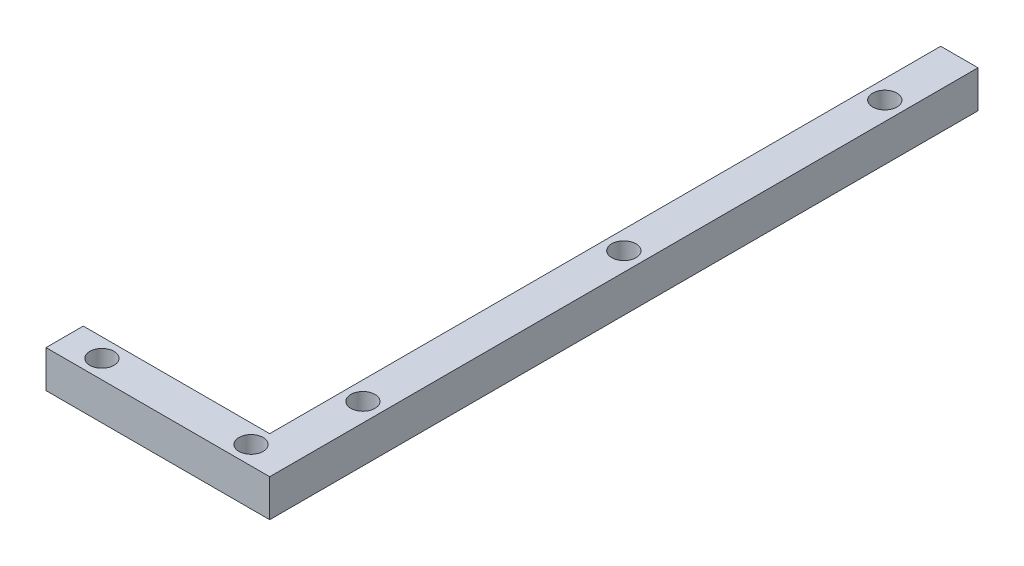
SolidWorks part; units mm, degrees
ref_plane "Front Plane" through (0, 0, 0) normal (0, 0, 1) x (1, 0, 0)
ref_plane "Top Plane" through (0, 0, 0) normal (0, 1, 0) x (1, 0, 0)
ref_plane "Right Plane" through (0, 0, 0) normal (1, 0, 0) x (0, 0, -1)
sketch "Sketch1" plane through (0, 0, 0) normal (0, 1, 0) x (1, 0, 0)
  line L0 (0, 0) -> (0, 180)
  line L1 (0, 180) -> (10, 180)
  line L2 (10, 180) -> (10, -10)
  line L3 (10, -10) -> (-50, -10)
  line L4 (-50, -10) -> (-50, 0)
  line L5 (-50, 0) -> (0, 0)
  dimension "D1" = 10
  dimension "D2" = 10
  dimension "D3" = 180
  dimension "D4" = 60
extrude "Boss-Extrude1" add sketch "Sketch1" along normal blind 10 contours L2 L3 L4 L5 L0 L1
sketch "Sketch2" plane through (0, 10, 0) normal (0, 1, 0) x (1, 0, 0)
  line L0 (0, 180) -> (10, 180) construction
  line L1 (-50, 0) -> (0, 0) construction
  line L2 (10, 180) -> (10, -10) construction
  line L3 (-50, -10) -> (-50, 0) construction
  line L4 (10, -10) -> (-50, -10) construction
  line L5 (0, 0) -> (0, 180) construction
  circle A0 centre (5, 160) radius 3.25
  circle A1 centre (5, 90) radius 3.25
  circle A2 centre (5, 20) radius 3.25
  circle A3 centre (-40, -5) radius 3.25
  circle A4 centre (0, -5) radius 3.25
  point P18 (-50, -5)
  dimension "D6" = 6.5
  dimension "D7" = 6.5
  dimension "D8" = 6.5
  dimension "D9" = 6.5
  dimension "D10" = 6.5
  dimension "D1" = 20
  dimension "D2" = 20
  dimension "D3" = 10
  dimension "D4" = 10
  dimension "D5" = 70
  dimension "D11" = 5
  dimension "D12" = 5
  dimension "D13" = 5
  dimension "D14" = 5
  dimension "D15" = 5
extrude "Cut-Extrude1" cut sketch "Sketch2" against normal through all
